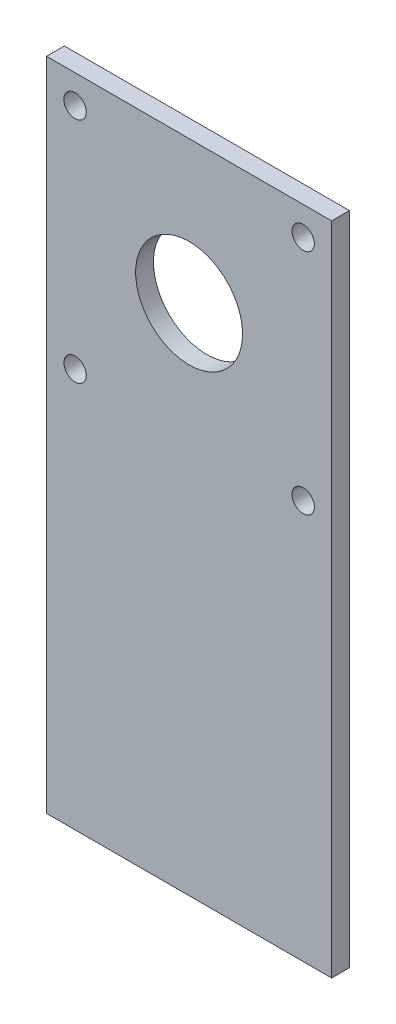
SolidWorks part; units mm, degrees
ref_plane "Front Plane" through (0, 0, 0) normal (0, 0, 1) x (1, 0, 0)
ref_plane "Top Plane" through (0, 0, 0) normal (0, 1, 0) x (1, 0, 0)
ref_plane "Right Plane" through (0, 0, 0) normal (1, 0, 0) x (0, 0, -1)
sketch "Sketch2" plane through (0, 0, 0) normal (0, 0, 1) x (1, 0, 0)
  line L1 (0, 0) -> (50.8, 0)
  line L2 (0, 0) -> (0, 50.8)
  line L3 (0, 50.8) -> (50.8, 50.8)
  line L4 (50.8, 0) -> (50.8, 50.8)
  circle A0 centre (5.08, 45.72) radius 2
  circle A1 centre (45.72, 45.72) radius 2
  circle A2 centre (45.72, 5.08) radius 2
  circle A3 centre (5.08, 5.08) radius 2
  circle A4 centre (25.4, 25.4) radius 9.525
  dimension "D3" = 4
  dimension "D6" = 19.05
  dimension "D1" = 50.8
  dimension "D2" = 50.8
  dimension "D4" = 5.08
  dimension "D5" = 5.08
  dimension "D7" = 5.08
  dimension "D8" = 5.08
extrude "Boss-Extrude1" add sketch "Sketch2" along normal blind 3.175
sketch "Sketch3" plane through (0, 0, 0) normal (0, -1, 0) x (1, 0, 0)
  line L1 (0, 3.175) -> (50.8, 3.175)
  line L2 (0, 3.175) -> (0, 0)
  line L3 (0, 0) -> (50.8, 0)
  line L4 (50.8, 3.175) -> (50.8, 0)
extrude "Boss-Extrude2" add sketch "Sketch3" along normal blind 66.04
